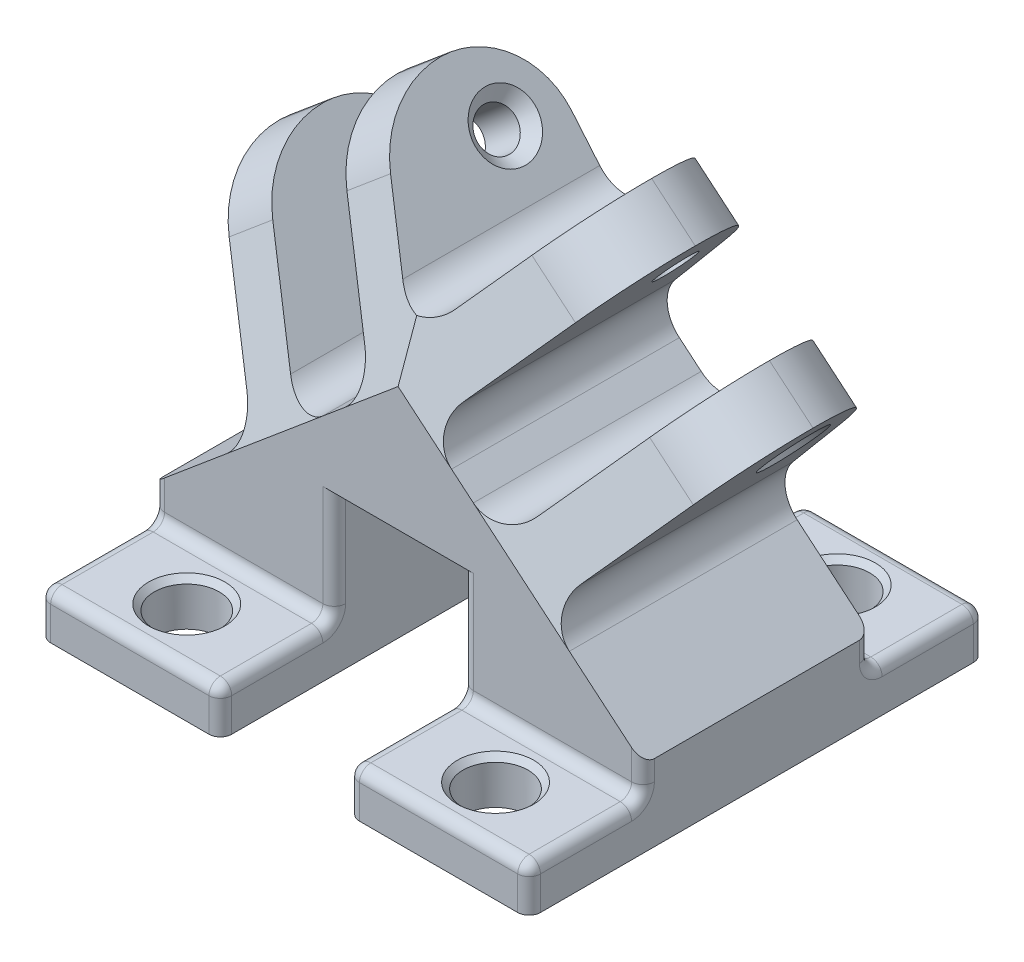
SolidWorks part; units mm, degrees
material "ABS"
ref_plane "Front Plane" through (0, 0, 0) normal (0, 0, 1) x (1, 0, 0)
ref_plane "Top Plane" through (0, 0, 0) normal (0, 1, 0) x (1, 0, 0)
ref_plane "Right Plane" through (0, 0, 0) normal (1, 0, 0) x (0, 0, -1)
sketch "Sketch1" plane through (0, 0, 0) normal (0, 0, 1) x (1, 0, 0)
  line L0 (0, 0) -> (-16.5, 0)
  line L1 (-16.5, 0) -> (0, 13.8451)
  line L2 (0, 13.8451) -> (0, 0) construction
  line L3 (0, 13.8451) -> (10, 13.8451)
  line L4 (5, 13.8451) -> (5, 0) construction
  line L5 (10, 0) -> (26.5, 0)
  line L6 (10, 13.8451) -> (10, 0) construction
  line L7 (26.5, 0) -> (10, 13.8451)
  line L8 (4.516, 13.8451) -> (-7.6475, 28.341) construction
  line L9 (-7.6475, 31.091) -> (-6.2588, 32.2563) construction
  line L10 (-10.3975, 28.341) -> (-11.7862, 27.1758) construction
  line L11 (-7.6475, 28.341) -> (-9.4152, 30.4477) construction
  line L12 (-7.6475, 28.341) -> (-9.7541, 26.5734) construction
  line L13 (-4.9393, 27.8635) -> (-3.5506, 29.0288) construction
  line L14 (-8.125, 25.6328) -> (-9.5138, 24.4675) construction
  line L15 (-11.7862, 27.1758) -> (-9.5138, 24.4675) construction
  line L16 (-3.5506, 29.0288) -> (-6.2588, 32.2563) construction
  line L17 (-8.0879, 35.4776) -> (-0.6958, 26.6681)
  line L18 (-7.6475, 28.341) -> (-1.1361, 33.8047) construction
  line L19 (-9.4152, 30.4477) -> (-7.841, 31.7686) construction
  line L20 (-14.5992, 30.0139) -> (-7.2072, 21.2044)
  line L21 (-0.6958, 26.6681) -> (5, 19.8801)
  line L22 (-7.2072, 21.2044) -> (-0.6056, 13.337)
  line L23 (0, 13.8451) -> (5, 18.0406)
  line L24 (5, 18.0406) -> (5, 19.8801)
  line L25 (26.5, 0) -> (10, 13.8451)
  line L26 (10, 13.8451) -> (5, 18.0406)
  line L27 (19.4152, 30.4477) -> (17.841, 31.7686) construction
  line L28 (17.6475, 31.091) -> (16.2588, 32.2563) construction
  line L29 (17.6475, 28.341) -> (11.1361, 33.8047) construction
  line L30 (13.5506, 29.0288) -> (16.2588, 32.2563) construction
  line L31 (14.9393, 27.8635) -> (13.5506, 29.0288) construction
  line L32 (18.125, 25.6328) -> (19.5138, 24.4675) construction
  line L33 (21.7862, 27.1758) -> (19.5138, 24.4675) construction
  line L34 (20.3975, 28.341) -> (21.7862, 27.1758) construction
  line L35 (17.6475, 28.341) -> (19.4152, 30.4477) construction
  line L36 (17.6475, 28.341) -> (19.7541, 26.5734) construction
  line L37 (5.484, 13.8451) -> (17.6475, 28.341) construction
  line L38 (17.2072, 21.2044) -> (10.6056, 13.337)
  line L39 (10.6958, 26.6681) -> (5, 19.8801)
  line L40 (18.0879, 35.4776) -> (10.6958, 26.6681)
  line L41 (24.5992, 30.0139) -> (17.2072, 21.2044)
  line L42 (-3.9064, 17.2707) -> (-19.8008, 3.9337)
  line L43 (-19.8008, 3.9337) -> (-16.5, 0)
  line L44 (29.8008, 3.9337) -> (26.5, 0)
  line L45 (13.9064, 17.2707) -> (29.8008, 3.9337)
  line L46 (-14.5992, 30.0139) -> (-18.4295, 26.8)
  line L47 (-18.4295, 26.8) -> (-7.7366, 14.0568)
  line L48 (-8.0879, 35.4776) -> (-4.2576, 38.6916)
  line L49 (-4.2576, 38.6916) -> (5, 27.6588)
  line L50 (5, 27.6588) -> (5, 19.8801)
  line L51 (28.4295, 26.8) -> (17.7366, 14.0568)
  line L52 (24.5992, 30.0139) -> (28.4295, 26.8)
  line L53 (14.2576, 38.6916) -> (5, 27.6588)
  line L54 (18.0879, 35.4776) -> (14.2576, 38.6916)
  line L55 (-3.9064, 17.2707) -> (2.605, 22.7344)
  line L56 (13.9064, 17.2707) -> (7.395, 22.7344)
  line L57 (-0.6056, 13.337) -> (-0.6056, 0)
  line L58 (10.6056, 13.337) -> (10.6056, 0)
  line L59 (0, 13.8451) -> (-0.6056, 13.8451)
  line L60 (-0.6056, 13.8451) -> (-0.6056, 13.337)
  line L61 (10, 13.8451) -> (10.6056, 13.8451)
  line L62 (10.6056, 13.8451) -> (10.6056, 13.337)
  circle A0 centre (-7.6475, 28.341) radius 2.75 construction
  circle A1 centre (17.6475, 28.341) radius 2.75 construction
  point P24 (-4.3918, 31.0729)
  dimension "D6" = 5.5
  dimension "D1" = 21.5392
  dimension "D2" = 40
  dimension "D3" = 10
  dimension "D4" = 0.484
  dimension "D5" = 18.923
  dimension "D7" = 7.5
  dimension "D8" = 3
  dimension "D9" = 4.25
  dimension "D10" = 5
  dimension "D11" = 5
  dimension "D12" = 5.75
  dimension "D13" = 15.8944
extrude "Boss-Extrude1" add sketch "Sketch1" along normal blind 20 contours L2 L1 L0 | L5 L7 L25 L6 | L42 L43 L1 L22 | L46 L47 L42 L22 L20 | L55 L22 L1 L23 L24 L21 | L38 L56 L39 L24 L26 L25 | L3 L26 L23 | L50 L49 L48 L17 L21 | L40 L54 L53 L50 L39 | L52 L41 L38 L45 L51 | L45 L38 L7 L44
sketch "Sketch5" plane through (2.3816, 1.9984, 0) normal (-0.766, -0.6428, 0) x (0, 0, 1)
  line L0 (5.0261, 32.3762) -> (5.0261, 15.7411) construction
  line L1 (20, 32.3762) -> (0, 32.3762) construction
  line L2 (20, 15.7411) -> (0, 15.7411) construction
  line L3 (0, 32.3762) -> (0, 15.7411) construction
  line L4 (-0.55, 32.3762) -> (-0.55, 15.7411) construction
  circle A0 centre (5.0261, 26.6242) radius 1.75
  dimension "D3" = 3.5
  dimension "D1" = 5.5761
  dimension "D2" = 0.55
  dimension "D4" = 5.752
extrude "Cut-Extrude3" cut sketch "Sketch5" against normal through all
sketch3d "3DSketch1"
  line L0 (-0.6056, 13.8451, 20) -> (10.6056, 13.8451, 20) construction
  line L1 (-0.6056, 13.8451, 20) -> (10.6056, 13.8451, 20)
  point P2 (5, 13.8451, 20)
sketch "Sketch6" plane through (3.4867, -2.9257, 0) normal (0.766, -0.6428, 0) x (0, 0, -1)
  line L0 (-5.0261, 38.8041) -> (-5.0261, 22.169) construction
  line L1 (-20, 38.8041) -> (0, 38.8041) construction
  line L2 (-20, 22.169) -> (0, 22.169) construction
  line L3 (-20, 33.0521) -> (0, 33.0521) construction
  line L4 (-20, 38.8041) -> (-20, 22.169) construction
  line L5 (0, 38.8041) -> (0, 22.169) construction
  line L6 (0.55, 38.8041) -> (0.55, 22.169) construction
  circle A0 centre (-5.0261, 33.0521) radius 1.75
  dimension "D3" = 3.5
  dimension "D1" = 5.5761
  dimension "D2" = 5.752
  dimension "D4" = 0.55
extrude "Cut-Extrude4" cut sketch "Sketch6" against normal through all
sketch "Sketch7" plane through (2.3816, 1.9984, 0) normal (-0.766, -0.6428, 0) x (0, 0, 1)
  line L0 (20, 32.3762) -> (0, 32.3762) construction
  line L1 (0, 32.3762) -> (0, 15.7411) construction
  line L3 (14.4587, 27.6245) -> (20, 15.7411)
  line L4 (20, 32.3762) -> (20, 15.7411) construction
  line L5 (20, 15.7411) -> (0, 15.7411) construction
  line L6 (0, 25.3762) -> (0, 32.3762)
  line L7 (0, 32.3762) -> (7, 32.3762)
  line L8 (7, 32.3762) -> (20, 32.3762)
  line L9 (20, 32.3762) -> (20, 15.7411)
  arc A0 (7, 32.3762) -> (0, 25.3762) centre (7, 25.3762) ccw
  arc A1 (7, 32.3762) -> (14.4587, 27.6245) centre (7, 24.1465) cw
  line M3 (0, 32.3762) -> (0, 15.7411)
  line M5 (20, 15.7411) -> (20, 32.3762)
  line M6 (20, 32.3762) -> (0, 32.3762)
  dimension "D1" = 7
  dimension "D2" = 65
extrude "Cut-Extrude5" cut sketch "Sketch7" against normal through all contours A0 M6 M3 | A1 L3 M6 M5
sketch "Sketch8" plane through (3.4867, -2.9257, 0) normal (0.766, -0.6428, 0) x (0, 0, -1)
  line L0 (-20, 38.8041) -> (0, 38.8041) construction
  line L1 (0, 38.8041) -> (0, 22.169) construction
  line L2 (-14.4587, 34.0524) -> (-20, 22.169)
  line L3 (-20, 22.169) -> (0, 22.169) construction
  line L4 (-20, 22.169) -> (-20, 38.8041)
  line L5 (-20, 38.8041) -> (-7, 38.8041)
  line L6 (-7, 38.8041) -> (0, 38.8041)
  line L7 (0, 38.8041) -> (0, 31.8041)
  arc A0 (-7, 38.8041) -> (0, 31.8041) centre (-7, 31.8041) cw
  arc A1 (-7, 38.8041) -> (-14.4587, 34.0524) centre (-7, 30.5744) ccw
  line M3 (0, 22.169) -> (0, 38.8041)
  line M4 (0, 38.8041) -> (-20, 38.8041)
  line M5 (-20, 38.8041) -> (-20, 22.169)
  dimension "D1" = 7
  dimension "D2" = 65
extrude "Cut-Extrude6" cut sketch "Sketch8" against normal through all contours A1 L2 M4 M5 | A0 M4 M3
sketch "Sketch9" plane through (0, 0, 20) normal (0, 0, 1) x (1, 0, 0)
  line L0 (-0.6056, 0) -> (-16.5, 0) construction
  line L1 (-0.6056, 0) -> (-16.5, 0)
  line L2 (5, 13.8451) -> (5, 0) construction
  line L3 (-19.8008, 3.9337) -> (-16.5, 0) construction
  line L4 (-19.8008, 3.9337) -> (-16.5, 0)
  line L5 (-19.8008, 3.9337) -> (-0.6056, 3.9337)
  line L6 (-0.6056, 13.8451) -> (-0.6056, 0) construction
  line L7 (-0.6056, 3.9337) -> (-0.6056, 0)
  line L8 (10.6056, 3.9337) -> (10.6056, 0)
  line L9 (29.8008, 3.9337) -> (10.6056, 3.9337)
  line L10 (10.6056, 0) -> (26.5, 0)
  line L11 (29.8008, 3.9337) -> (26.5, 0)
  point P5 (-8.5528, 0)
extrude "Boss-Extrude3" add sketch "Sketch9" along normal blind 10
sketch "Sketch10" plane through (0, 3.9337, 0) normal (0, 1, 0) x (1, 0, 0)
  line L0 (-10.2032, -20) -> (-10.2032, -30) construction
  line L1 (-0.6056, -20) -> (-19.8008, -20) construction
  line L2 (-0.6056, -30) -> (-19.8008, -30) construction
  line L3 (-19.8008, -25) -> (-0.6056, -25) construction
  line L4 (-19.8008, -30) -> (-19.8008, -20) construction
  line L5 (-0.6056, -30) -> (-0.6056, -20) construction
  line L6 (5, -20) -> (5, -30) construction
  line L7 (-16.5, -30) -> (-0.6056, -30) construction
  line L8 (-16.5, -30) -> (-0.6056, -30)
  line L9 (-8.5528, -30) -> (-8.5528, -20) construction
  circle A1 centre (-8.5528, -25) radius 2.85
  circle A2 centre (18.5528, -25) radius 2.85
  dimension "D1" = 5.7
extrude "Cut-Extrude7" cut sketch "Sketch10" against normal through all contours A1 | A2
sketch "Sketch11" plane through (0, 0, 0) normal (0, 0, -1) x (-1, 0, 0)
  line L0 (19.8008, 3.9337) -> (16.5, 0) construction
  line L1 (0.6056, 0) -> (16.5, 0) construction
  line L2 (0.6056, 3.9337) -> (0.6056, 0) construction
  line L3 (19.8008, 3.9337) -> (0.6056, 3.9337) construction
  line L4 (-10.6056, 3.9337) -> (-10.6056, 0) construction
  line L5 (-10.6056, 0) -> (-26.5, 0) construction
  line L6 (-29.8008, 3.9337) -> (-26.5, 0) construction
  line L7 (-29.8008, 3.9337) -> (-10.6056, 3.9337) construction
  line L8 (19.8008, 3.9337) -> (16.5, 0)
  line L9 (0.6056, 0) -> (16.5, 0)
  line L10 (0.6056, 3.9337) -> (0.6056, 0)
  line L11 (19.8008, 3.9337) -> (0.6056, 3.9337)
  line L12 (-10.6056, 3.9337) -> (-10.6056, 0)
  line L13 (-10.6056, 0) -> (-26.5, 0)
  line L14 (-29.8008, 3.9337) -> (-26.5, 0)
  line L15 (-29.8008, 3.9337) -> (-10.6056, 3.9337)
extrude "Boss-Extrude4" add sketch "Sketch11" along normal blind 10
sketch "Sketch12" plane through (0, 3.9337, 0) normal (0, 1, 0) x (1, 0, 0)
  line L0 (-0.6056, 10) -> (-16.5, 10) construction
  line L1 (-0.6056, 10) -> (-16.5, 10)
  line L2 (-8.5528, 10) -> (-8.5528, 0) construction
  line L3 (-19.8008, 0) -> (-0.6056, 0) construction
  line L4 (5, -20) -> (5, -30) construction
  line L5 (5, -20) -> (5, -30)
  circle A0 centre (-8.5528, 5) radius 2.85
  circle A1 centre (18.5528, 5) radius 2.85
  dimension "D1" = 5.7
extrude "Cut-Extrude8" cut sketch "Sketch12" against normal through all contours L2 A0 | A1 | A0 L2
sketch "Sketch13" plane through (0, 0, 30) normal (0, 0, 1) x (1, 0, 0)
  line L0 (5, 13.8451) -> (5, 0) construction
  line L1 (-0.6056, 13.8451) -> (10.6056, 13.8451) construction
  line L3 (-16.5, 0) -> (-16.5, 3.9337)
  line L4 (-0.6056, 3.9337) -> (-19.8008, 3.9337) construction
  line L7 (-16.5, 3.9337) -> (-16.5, 6.7034)
  line L8 (-7.7366, 14.0568) -> (-19.8008, 3.9337) construction
  line L9 (-16.5, 6.7034) -> (-19.8008, 3.9337)
  line L10 (-19.8008, 3.9337) -> (-16.5, 0)
  line L11 (26.5, 0) -> (26.5, 3.9337)
  line L12 (29.8008, 3.9337) -> (26.5, 0)
  line L13 (26.5, 3.9337) -> (26.5, 6.7034)
  line L14 (26.5, 6.7034) -> (29.8008, 3.9337)
extrude "Cut-Extrude9" cut sketch "Sketch13" against normal through all
chamfer "Chamfer1" distance 1 angle 45 4 edges at (25.857, 23.7343, 5.0261) (11.6852, 35.6259, 5.0261) (-13.6073, 21.0531, 5.0261) (-1.6852, 35.6259, 5.0261)
chamfer "Chamfer2" distance 0.5 angle 45 4 edges at (18.5528, 3.9337, 27.85) (18.5528, 3.9337, -2.15) (-8.5528, 3.9337, -2.15) (-8.5528, 3.9337, 27.85)
fillet "Fillet1" radius 1 32 edges at (26.5, 5.3186, 20) (10.6056, 8.8894, 20) (-0.6056, 8.8894, 20) (-16.5, 5.3186, 20) (26.5, 1.9669, 30) (26.5, 3.9337, 25) (18.5528, 3.9337, 30) (18.5528, 3.9337, 20) (10.6056, 1.9669, 30) (10.6056, 3.9337, 25) (-8.5528, 3.9337, 20) (-8.5528, 3.9337, 30) (-16.5, 3.9337, 25) (-16.5, 1.9669, 30) (-0.6056, 1.9669, 30) (-0.6056, 3.9337, 25) (26.5, 5.3186, 0) (10.6056, 8.8894, 0) (-0.6056, 8.8894, 0) (-16.5, 5.3186, 0) (26.5, 3.9337, -5) (26.5, 1.9669, -10) (18.5528, 3.9337, 0) (18.5528, 3.9337, -10) (10.6056, 1.9669, -10) (10.6056, 3.9337, -5) (-0.6056, 1.9669, -10) (-0.6056, 3.9337, -5) (-8.5528, 3.9337, -10) (-8.5528, 3.9337, 0) (-16.5, 1.9669, -10) (-16.5, 3.9337, -5)
fillet "Fillet2" radius 3 7 edges at (17.7366, 14.0568, 10) (13.9064, 17.2707, 10) (7.395, 22.7344, 10) (5, 27.6588, 9.4794) (2.605, 22.7344, 10) (-3.9064, 17.2707, 10) (-7.7366, 14.0568, 10)
sketch3d "3DSketch3"
  line L0 (-1.6056, 13.8451, 20) -> (11.6056, 13.8451, 20) construction
  line L1 (-1.6056, 13.8451, 20) -> (11.6056, 13.8451, 20)
  point P2 (5, 13.8451, 20)
sketch3d "3DSketch4"
  line L0 (10.5603, 34.2853, 5.0261) -> (24.7321, 22.3937, 5.0261)
  line L1 (-0.5603, 34.2853, 5.0261) -> (-14.7321, 22.3937, 5.0261)
  circle A0 centre (24.7321, 22.3937, 5.0261) radius 2.75 construction
  circle A1 centre (10.5603, 34.2853, 5.0261) radius 2.75 construction
  circle A2 centre (24.7321, 22.3937, 5.0261) radius 2.75
  circle A3 centre (10.5603, 34.2853, 5.0261) radius 2.75
  circle A4 centre (-14.7321, 22.3937, 5.0261) radius 2.75 construction
  circle A5 centre (-0.5603, 34.2853, 5.0261) radius 2.75 construction
  circle A6 centre (-14.7321, 22.3937, 5.0261) radius 2.75
  circle A7 centre (-0.5603, 34.2853, 5.0261) radius 2.75
  point P2 (22.6255, 24.1614, 5.0261)
  point P5 (12.6669, 32.5176, 5.0261)
  point P7 (22.6255, 24.1614, 5.0261)
  point P9 (12.6669, 32.5176, 5.0261)
  point P10 (17.6462, 28.3395, 5.0261)
  point P13 (-12.6255, 24.1614, 5.0261)
  point P16 (-2.6669, 32.5176, 5.0261)
  point P18 (-12.6255, 24.1614, 5.0261)
  point P20 (-2.6669, 32.5176, 5.0261)
  point P21 (-7.6462, 28.3395, 5.0261)
